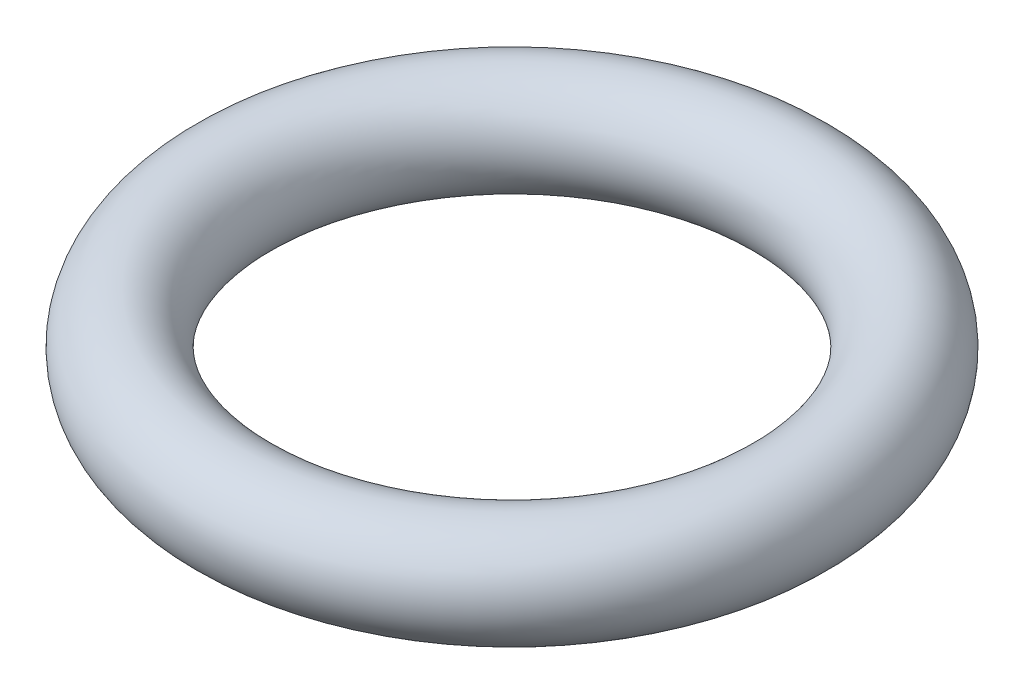
SolidWorks part; units mm, degrees
ref_plane "Front Plane" through (0, 0, 0) normal (0, 0, 1) x (1, 0, 0)
ref_plane "Top Plane" through (0, 0, 0) normal (0, 1, 0) x (1, 0, 0)
ref_plane "Right Plane" through (0, 0, 0) normal (1, 0, 0) x (0, 0, -1)
sketch "Sketch3" plane through (0, 0, 0) normal (0, 0, 1) x (1, 0, 0)
  line L0 (0, 0) -> (0, 2.7576)
  circle A0 centre (4, 0) radius 0.75
  dimension "D2" = 1.5
  dimension "D1" = 4
revolve "Revolve1" add sketch "Sketch3" angle 360 about L0
